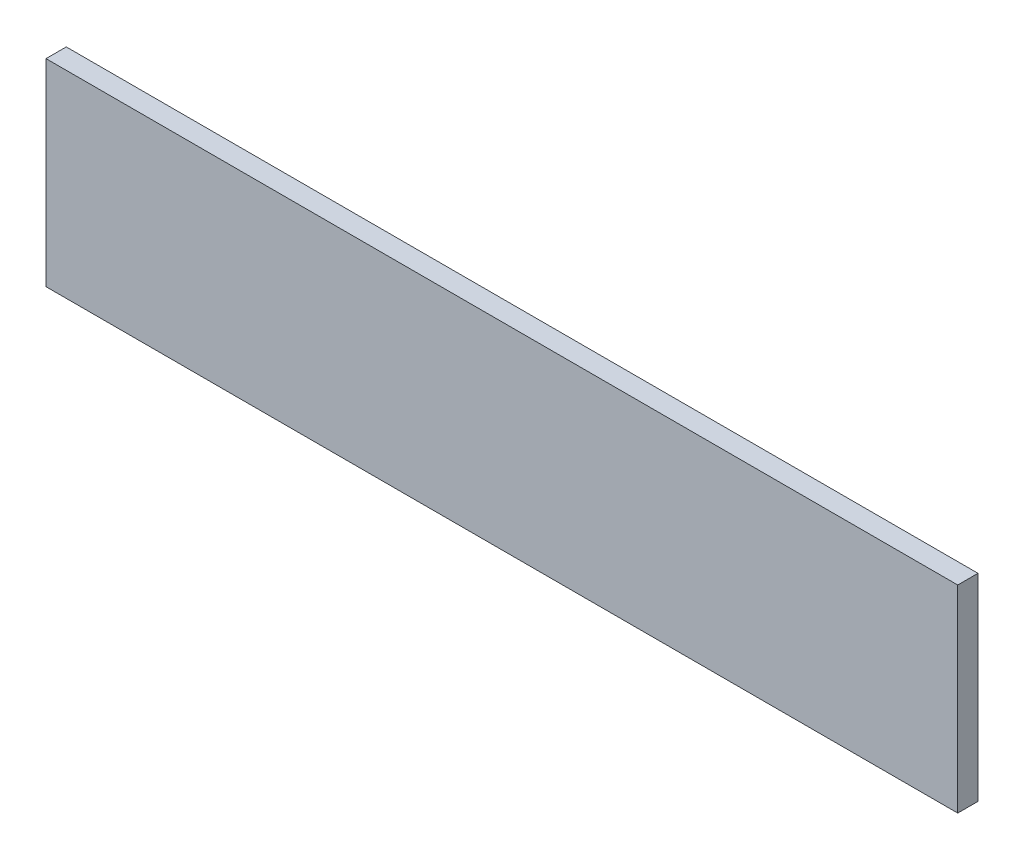
SolidWorks part; units mm, degrees
ref_plane "Alzado" through (0, 0, 0) normal (0, 0, 1) x (1, 0, 0)
ref_plane "Planta" through (0, 0, 0) normal (0, 1, 0) x (1, 0, 0)
ref_plane "Vista lateral" through (0, 0, 0) normal (1, 0, 0) x (0, 0, -1)
sketch "Croquis1" plane through (0, 0, 0) normal (0, 0, 1) x (1, 0, 0)
  line L1 (-516.4408, 330.2661) -> (383.5592, 330.2661)
  line L2 (-516.4408, 330.2661) -> (-516.4408, 135.2661)
  line L3 (-516.4408, 135.2661) -> (383.5592, 135.2661)
  line L4 (383.5592, 330.2661) -> (383.5592, 135.2661)
  dimension "D1" = 900
  dimension "D2" = 195
extrude "Saliente-Extruir1" add sketch "Croquis1" along normal blind 20
